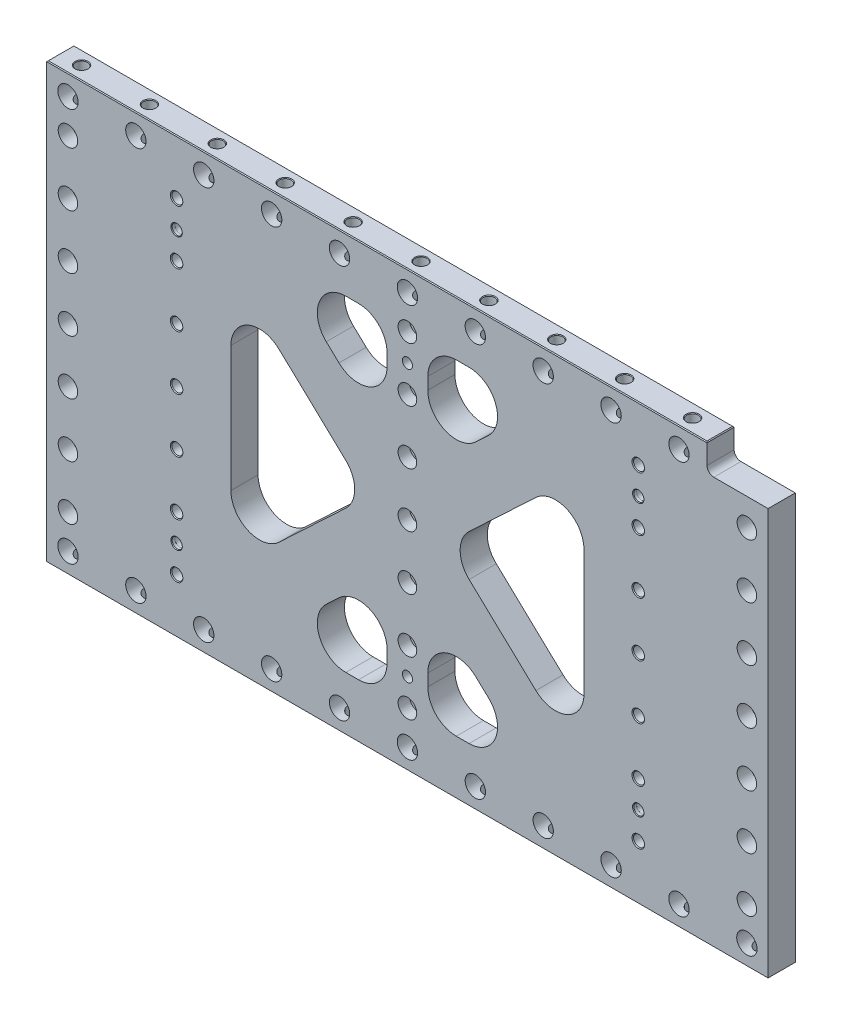
SolidWorks part; units mm, degrees
material "6061-T6 Al"
ref_plane "Front Plane" through (0, 0, 0) normal (0, 0, 1) x (1, 0, 0)
ref_plane "Top Plane" through (0, 0, 0) normal (0, 1, 0) x (1, 0, 0)
ref_plane "Right Plane" through (0, 0, 0) normal (1, 0, 0) x (0, 0, -1)
sketch "Sketch2" plane through (0, 0, 0) normal (0, 0, 1) x (1, 0, 0)
  line L0 (-337.3437, -203.2) -> (337.3437, 203.2) construction
  line L1 (-337.3438, 203.2) -> (337.3437, 203.2)
  line L2 (-337.3438, 203.2) -> (-337.3437, -203.2)
  line L3 (-337.3437, -203.2) -> (337.3437, -203.2)
  line L4 (337.3437, 203.2) -> (337.3437, -203.2)
  point P4 (0, 0)
  dimension "D1" = 674.6875
  dimension "D2" = 406.4
extrude "Extrude1" add sketch "Sketch2" along normal mid plane 25.4
hole_wizard "CBORE for 3/8 Socket Head Cap Screw3" positions "Sketch4" profile "Sketch3" counterbore size "3/8" standard "Ansi Inch" end condition through all
sketch "Sketch4" plane through (-149.0359, 144.1868, -12.7) normal (0, 0, 1) x (1, 0, 0)
  line L3 (149.0359, -144.1868) -> (-66.8641, -144.1868) construction
  line L8 (149.0359, -144.1868) -> (364.9359, -144.1868) construction
  point P34 (-66.8641, -144.1868)
  dimension "D1" = 431.8
sketch "Sketch3" plane through (-215.9, 0, -12.7) normal (1, 0, 0) x (0, 1, 0)
  line L0 (0, 0) -> (0, 25.4)
  line L1 (5.1587, 24.614) -> (5.842, 25.4)
  line L2 (5.1587, 24.614) -> (5.1587, 10.668)
  line L3 (5.1587, 10.668) -> (8.7312, 10.668)
  line L4 (8.7312, 10.668) -> (8.7312, 0)
  line L5 (8.7312, 0) -> (0, 0)
  line L11 (0, -6.35) -> (0, 107.95) construction
  line L12 (5.842, 25.4) -> (0, 25.4)
  line L13 (-5.1587, 24.614) -> (-5.842, 25.4) construction
  dimension "Thru Hole Dia." = 10.3175
  dimension "Thru Hole Depth" = 25.4
  dimension "C'Bore Dia." = 17.4625
  dimension "C'Bore Depth" = 10.668
  dimension "Far C'Sink Dia." = 11.684
  dimension "Far C'Sink Angle" = 82
pattern_linear "LPattern3" count 4 spacing 50.8 along (0, 1, 0) count 4 spacing 50.8 along (0, -1, 0) of "CBORE for 3/8 Socket Head Cap Screw3"
mirror "Mirror1" about plane through (0, 0, 0) normal (1, 0, 0) of "CBORE for 3/8 Socket Head Cap Screw3", "LPattern3"
sketch "Sketch8" plane through (0, 0, 12.7) normal (0, 0, 1) x (1, 0, 0)
  line L1 (-337.3437, -203.2) -> (337.3437, -203.2) construction
  line L2 (-165.1, 120.5077) -> (-37.0606, 0)
  line L3 (-37.0606, 0) -> (-165.1, -120.5077)
  line L4 (-165.1, -120.5077) -> (-165.1, 120.5077)
  line L5 (-124.8644, 152.4) -> (0, 34.8805)
  line L6 (0, 34.8805) -> (124.8644, 152.4)
  line L7 (124.8644, 152.4) -> (-124.8644, 152.4)
  line L8 (165.1, 120.5077) -> (165.1, -120.5077)
  line L9 (165.1, -120.5077) -> (37.0606, 0)
  line L10 (37.0606, 0) -> (165.1, 120.5077)
  line L11 (0, -34.8805) -> (-124.8644, -152.4)
  line L12 (-124.8644, -152.4) -> (124.8644, -152.4)
  line L13 (124.8644, -152.4) -> (0, -34.8805)
  line L15 (215.9, -203.2) -> (-215.9, 203.2) construction
  line L16 (-215.9, 203.2) -> (-215.9, 101.6) construction
  line L17 (0, 0) -> (37.0606, 0) construction
  line L18 (0, 34.8805) -> (0, 0) construction
  line L19 (0, 0) -> (-37.0606, 0) construction
  line L20 (0, -34.8805) -> (0, 0) construction
  line L21 (337.3437, 203.2) -> (-337.3438, 203.2) construction
  line L22 (-215.9, -101.6) -> (-215.9, -203.2) construction
  line L23 (-215.9, -203.2) -> (215.9, 203.2) construction
  line L24 (215.9, 203.2) -> (215.9, 101.6) construction
  dimension "D1" = 50.8
  dimension "D2" = 50.8
  dimension "D3" = 50.8
  dimension "D4" = 431.8
extrude "Triangles -- Cut-Extrude2" cut sketch "Sketch8" against normal through all
fillet "Triangles -- Fillet1" radius 26.67 12 edges at (-165.1, -120.5077, 0) (-37.0606, 0, 0) (-124.8644, -152.4, 0) (124.8644, -152.4, 0) (0, -34.8805, 0) (37.0606, 0, 0) (165.1, -120.5077, 0) (165.1, 120.5077, 0) (124.8644, 152.4, 0) (-124.8644, 152.4, 0) (0, 34.8805, 0) (-165.1, 120.5077, 0)
sketch "Sketch14" plane through (0, 0, 12.7) normal (0, 0, 1) x (1, 0, 0)
  line L0 (337.3437, 203.2) -> (-337.3438, 203.2) construction
  line L1 (-19.05, 203.2) -> (19.05, 203.2)
  line L2 (-19.05, 203.2) -> (-19.05, -203.2)
  line L3 (-19.05, -203.2) -> (19.05, -203.2)
  line L4 (19.05, 203.2) -> (19.05, -203.2)
  line L5 (-337.3437, -203.2) -> (337.3437, -203.2) construction
  line L6 (-19.05, 0) -> (19.05, 0) construction
  point P10 (0, 0)
  dimension "D1" = 38.1
extrude "Extrude5" add sketch "Sketch14" against normal through all
fillet "Fillet3" radius 26.67 8 edges at (19.05, -152.4, 0) (-19.05, -152.4, 0) (19.05, 152.4, 0) (-19.05, 152.4, 0) (-19.05, -52.8099, 0) (19.05, -52.8099, 0) (19.05, 52.8099, 0) (-19.05, 52.8099, 0)
hole_wizard "CBORE for 3/8 Socket Head Cap Screw2" positions "Sketch16" profile "Sketch15" counterbore size "3/8" standard "Ansi Inch" end condition through all
sketch "Sketch16" plane through (0, 0, 12.7) normal (0, 0, 1) x (1, 0, 0)
  point P1 (0, 0)
sketch "Sketch15" plane through (0, 0, 12.7) normal (1, 0, 0) x (0, -1, 0)
  line L0 (0, 0) -> (0, 25.4)
  line L1 (5.1587, 24.614) -> (5.842, 25.4)
  line L2 (5.1587, 24.614) -> (5.1587, 10.668)
  line L3 (5.1587, 10.668) -> (8.7312, 10.668)
  line L4 (8.7312, 10.668) -> (8.7312, 0)
  line L5 (8.7312, 0) -> (0, 0)
  line L11 (0, -6.35) -> (0, 107.95) construction
  line L12 (5.842, 25.4) -> (0, 25.4)
  line L13 (-5.1587, 24.614) -> (-5.842, 25.4) construction
  dimension "Thru Hole Dia." = 10.3175
  dimension "Thru Hole Depth" = 25.4
  dimension "C'Bore Dia." = 17.4625
  dimension "C'Bore Depth" = 10.668
  dimension "Far C'Sink Dia." = 11.684
  dimension "Far C'Sink Angle" = 82
pattern_linear "LPattern5" count 4 spacing 50.8 along (0, 1, 0) count 4 spacing 50.8 along (0, -1, 0) of "CBORE for 3/8 Socket Head Cap Screw2"
hole_wizard "3/4 (0.75) Diameter Hole1" positions "Sketch11" profile "Sketch10" hole size "3/4" standard "Ansi Inch" end condition through all
sketch "Sketch11" plane through (0, 0, 12.7) normal (0, 0, 1) x (1, 0, 0)
  line L0 (0, 0) -> (0, -184.15) construction
  line L2 (-337.3437, -203.2) -> (337.3437, -203.2) construction
  point P0 (0, -184.15)
  dimension "D1" = 19.05
sketch "Sketch10" plane through (0, -184.15, 12.7) normal (1, 0, 0) x (0, -1, 0)
  line L0 (0, 0) -> (0, 25.4)
  line L1 (0, 25.4) -> (9.525, 25.4)
  line L2 (9.525, 25.4) -> (9.525, 0)
  line L5 (9.525, 0) -> (0, 0)
  line L11 (0, -6.35) -> (0, 107.95) construction
  dimension "Thru Hole Dia." = 19.05
  dimension "Thru Hole Depth" = 25.4
hole_wizard "7/16 (0.4375) Diameter Hole1" positions "Sketch13" profile "Sketch12" hole size "7/16" standard "Ansi Inch"
sketch "Sketch13" plane through (0, -203.2, 0) normal (0, -1, 0) x (1, 0, 0)
  point P0 (0, 0)
sketch "Sketch12" plane through (0, -203.2, 0) normal (1, 0, 0) x (0, 0, -1)
  line L0 (0, 0) -> (0, 38.2635)
  line L1 (0, 38.2635) -> (5.5562, 34.925)
  line L2 (5.5562, 34.925) -> (5.5562, 0.6209)
  line L3 (5.5562, 0.6209) -> (6.096, 0)
  line L5 (6.096, 0) -> (0, 0)
  line L6 (-5.5562, 0.6209) -> (-6.096, 0) construction
  line L10 (0, 38.2635) -> (-5.5563, 34.925) construction
  line L11 (0, -6.35) -> (0, 107.95) construction
  dimension "Hole Dia." = 11.1125
  dimension "Hole Depth" = 34.925
  dimension "Near C'Sink Dia." = 12.192
  dimension "Near C'Sink Angle" = 82
  dimension "Drill Angle" = 118
pattern_linear "LPattern4" count 6 spacing 63.5 along (1, 0, 0) count 6 spacing 63.5 along (-1, 0, 0) of "7/16 (0.4375) Diameter Hole1", "3/4 (0.75) Diameter Hole1"
hole_wizard "3/4 (0.75) Diameter Hole2" positions "Sketch27" profile "Sketch26" hole size "3/4" standard "Ansi Inch" end condition through all
sketch "Sketch27" plane through (0, 0, 12.7) normal (0, 0, 1) x (1, 0, 0)
  line L0 (337.3437, 203.2) -> (-337.3438, 203.2) construction
  point P0 (0, 184.15)
  dimension "D1" = 19.05
sketch "Sketch26" plane through (0, 184.15, 12.7) normal (1, 0, 0) x (0, -1, 0)
  line L0 (0, 0) -> (0, 25.4)
  line L1 (0, 25.4) -> (9.525, 25.4)
  line L2 (9.525, 25.4) -> (9.525, 0)
  line L5 (9.525, 0) -> (0, 0)
  line L11 (0, -6.35) -> (0, 107.95) construction
  dimension "Thru Hole Dia." = 19.05
  dimension "Thru Hole Depth" = 25.4
hole_wizard "7/16 (0.4375) Diameter Hole2" positions "Sketch29" profile "Sketch28" hole size "7/16" standard "Ansi Inch"
sketch "Sketch29" plane through (0, 203.2, 0) normal (0, 1, 0) x (-1, 0, 0)
  point P0 (0, 0)
sketch "Sketch28" plane through (0, 203.2, 0) normal (1, 0, 0) x (0, 0, 1)
  line L0 (0, 0) -> (0, 38.2635)
  line L1 (0, 38.2635) -> (5.5562, 34.925)
  line L2 (5.5562, 34.925) -> (5.5562, 0.6209)
  line L3 (5.5562, 0.6209) -> (6.096, 0)
  line L5 (6.096, 0) -> (0, 0)
  line L6 (-5.5562, 0.6209) -> (-6.096, 0) construction
  line L10 (0, 38.2635) -> (-5.5563, 34.925) construction
  line L11 (0, -6.35) -> (0, 107.95) construction
  dimension "Hole Dia." = 11.1125
  dimension "Hole Depth" = 34.925
  dimension "Near C'Sink Dia." = 12.192
  dimension "Near C'Sink Angle" = 82
  dimension "Drill Angle" = 118
pattern_linear "LPattern6" count 6 spacing 63.5 along (-1, 0, 0) count 5 spacing 63.5 along (1, 0, 0) of "7/16 (0.4375) Diameter Hole2", "3/4 (0.75) Diameter Hole2"
sketch "Sketch17" plane through (0, 203.2, 0) normal (0, 1, 0) x (1, 0, 0)
  line L0 (337.3437, -12.7) -> (-337.3438, -12.7) construction
  line L1 (337.3437, 12.7) -> (280.1937, 12.7)
  line L2 (337.3437, 12.7) -> (337.3437, -12.7)
  line L3 (337.3437, -12.7) -> (280.1937, -12.7)
  line L4 (280.1937, 12.7) -> (280.1937, -12.7)
  dimension "D1" = 57.15
extrude "Cut-Extrude1" cut sketch "Sketch17" against normal blind 25.4
fillet "Fillet4" radius 6.35 1 edges at (280.1937, 177.8, 0)
hole_wizard "CBORE for 3/8 Socket Head Cap Screw1" positions "Sketch20" profile "Sketch19" counterbore size "3/8" standard "Ansi Inch" end condition through all
sketch "Sketch20" plane through (649.6365, 289.1507, 12.7) normal (0, 0, 1) x (1, 0, 0)
  line L0 (-967.1365, -441.5507) -> (-967.1365, -390.7507) construction
  line L1 (-967.1365, -390.7507) -> (-967.1365, -339.9507) construction
  line L2 (-967.1365, -339.9507) -> (-967.1365, -289.1507) construction
  line L3 (-967.1365, -289.1507) -> (-967.1365, -238.3507) construction
  line L4 (-967.1365, -238.3507) -> (-967.1365, -187.5507) construction
  line L5 (-967.1365, -187.5507) -> (-967.1365, -136.7507) construction
  line L8 (-986.9803, -492.3507) -> (-312.2928, -492.3507) construction
  point P1 (-967.1365, -136.7507)
  point P4 (-967.1365, -187.5507)
  point P7 (-967.1365, -238.3507)
  point P10 (-967.1365, -289.1507)
  point P13 (-967.1365, -339.9507)
  point P16 (-967.1365, -390.7507)
  point P19 (-967.1365, -441.5507)
  dimension "D1" = 50.8
  dimension "D2" = 317.5
  dimension "D3" = 50.8
sketch "Sketch19" plane through (-317.5, 152.4, 12.7) normal (1, 0, 0) x (0, -1, 0)
  line L0 (0, 0) -> (0, 25.4)
  line L1 (5.5562, 24.4869) -> (6.35, 25.4)
  line L2 (5.5562, 24.4869) -> (5.5562, 12.7)
  line L3 (5.5562, 12.7) -> (9.1281, 12.7)
  line L4 (9.1281, 12.7) -> (9.1281, 0)
  line L5 (9.1281, 0) -> (0, 0)
  line L11 (0, -6.35) -> (0, 107.95) construction
  line L12 (6.35, 25.4) -> (0, 25.4)
  line L13 (-5.5563, 24.4869) -> (-6.35, 25.4) construction
  dimension "Thru Hole Dia." = 11.1125
  dimension "Thru Hole Depth" = 25.4
  dimension "C'Bore Dia." = 18.2562
  dimension "C'Bore Depth" = 12.7
  dimension "Far C'Sink Dia." = 12.7
  dimension "Far C'Sink Angle" = 82
mirror "Mirror3" about plane through (0, 0, 0) normal (1, 0, 0) of "CBORE for 3/8 Socket Head Cap Screw1"
hole_wizard "3/8 (0.375) Pin + Lead-In Hole1" positions "Sketch22" profile "Sketch23" counterbore size "3/8" standard "Ansi Inch" end condition through all
sketch "Sketch22" plane through (82.5017, 186.7026, -12.7) normal (0, 0, -1) x (-1, 0, 0)
  line L4 (82.5017, -186.7026) -> (82.5017, -37.7471) construction
  line L7 (82.5017, -186.7026) -> (-55.0711, -186.7026) construction
  line L10 (-197.692, 16.4974) -> (419.8455, 16.4974) construction
  point P0 (82.5017, -59.7026)
  point P16 (82.5017, -313.7026)
  dimension "D1" = 76.2
sketch "Sketch23" plane through (0, 127, -12.7) normal (1, 0, 0) x (0, 1, 0)
  line L0 (0, 0) -> (0, 25.4)
  line L1 (0, 25.4) -> (4.7625, 25.4)
  line L3 (4.7625, 25.4) -> (4.7625, 3.175)
  line L4 (4.7879, 3.175) -> (4.7625, 3.175)
  line L5 (4.7879, 3.175) -> (4.7879, 0.6282)
  line L6 (4.7879, 0.6282) -> (5.334, 0)
  line L7 (5.334, 0) -> (0, 0)
  line L8 (-4.7879, 0.6282) -> (-5.334, 0) construction
  line L11 (0, -6.35) -> (0, 107.95) construction
  dimension "Thru Hole Dia." = 9.525
  dimension "Thru Hole Depth" = 25.4
  dimension "C'Bore Dia." = 9.5758
  dimension "C'Bore Depth" = 3.175
  dimension "Near C'Sink Dia." = 10.668
  dimension "Near C'Sink Angle" = 82
hole_wizard "3/8 (0.375) Pin + Lead-In Hole2" positions "Sketch25" profile "Sketch24" counterbore size "3/8" standard "Ansi Inch" end condition through all
sketch "Sketch25" plane through (0, 0, 12.7) normal (0, 0, 1) x (1, 0, 0)
  line L10 (0, 0) -> (86.482, 0) construction
  line L13 (0, 0) -> (0, 38.0076) construction
  line L16 (280.1937, 203.2) -> (-337.3438, 203.2) construction
  point P0 (-215.9, 127)
  point P1 (-215.9, -127)
  point P3 (215.9, -127)
  point P5 (215.9, 127)
  dimension "D1" = 431.8
  dimension "D2" = 76.2
sketch "Sketch24" plane through (-215.9, 127, 12.7) normal (1, 0, 0) x (0, -1, 0)
  line L0 (0, 0) -> (0, 25.4)
  line L1 (0, 25.4) -> (4.7625, 25.4)
  line L3 (4.7625, 25.4) -> (4.7625, 3.175)
  line L4 (4.7879, 3.175) -> (4.7625, 3.175)
  line L5 (4.7879, 3.175) -> (4.7879, 0.6282)
  line L6 (4.7879, 0.6282) -> (5.334, 0)
  line L7 (5.334, 0) -> (0, 0)
  line L8 (-4.7879, 0.6282) -> (-5.334, 0) construction
  line L11 (0, -6.35) -> (0, 107.95) construction
  dimension "Thru Hole Dia." = 9.525
  dimension "Thru Hole Depth" = 25.4
  dimension "C'Bore Dia." = 9.5758
  dimension "C'Bore Depth" = 3.175
  dimension "Near C'Sink Dia." = 10.668
  dimension "Near C'Sink Angle" = 82
chamfer "Chamfer1" distance 0.762 angle 45 8 edges at (0, -203.2, -12.7) (337.3437, -203.2, 0) (0, -203.2, 12.7) (-337.3437, -203.2, 0) (-337.3438, 203.2, 0) (-28.575, 203.2, -12.7) (280.1938, 203.2, 0) (-28.575, 203.2, 12.7)
